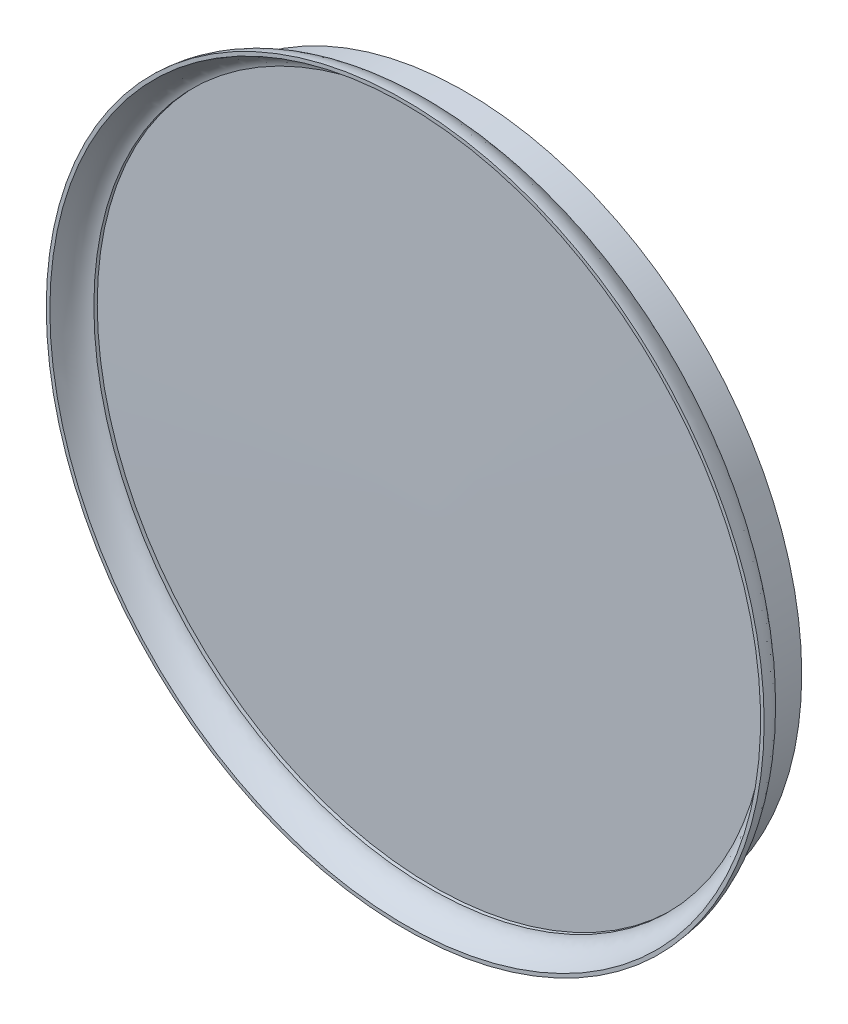
SolidWorks part; units mm, degrees
ref_plane "Front Plane" through (0, 0, 0) normal (0, 0, 1) x (1, 0, 0)
ref_plane "Top Plane" through (0, 0, 0) normal (0, 1, 0) x (1, 0, 0)
ref_plane "Right Plane" through (0, 0, 0) normal (1, 0, 0) x (0, 0, -1)
sketch "Sketch1" plane through (0, 0, 0) normal (0, 0, 1) x (1, 0, 0)
  circle A0 centre (0, 0) radius 44.75
  dimension "D1" = 89.5
extrude "Boss-Extrude1" add sketch "Sketch1" along normal blind 4
sketch "Sketch2" plane through (0, 0, 4) normal (0, 0, 1) x (1, 0, 0)
  circle A0 centre (0, 0) radius 47.75
  circle A1 centre (0, 0) radius 44.75 construction
  dimension "D1" = 3
extrude "Boss-Extrude2" add sketch "Sketch2" along normal blind 4
sketch "Sketch3" plane through (0, 0, 0) normal (1, 0, 0) x (0, 0, -1)
  line L0 (-4, -47.75) -> (-4, 47.75) construction
  line L1 (-4, -44.75) -> (-4, 44.75) construction
  line L2 (-4, 47.75) -> (-4, 44.75)
  line L3 (-4, 47.75) -> (-8, 47.75)
  line L4 (-14.6181, 0) -> (8.5023, 0) construction
  spline S0 degree 2 poles (-4, 44.75) (-5.5166, 47.7003) (-8, 47.75) knots 0 0 0 0.966898 0.966898 0.966898
revolve "Cut-Revolve1" cut sketch "Sketch3" angle 360 about L4
sketch "Sketch4" plane through (0, 0, 0) normal (1, 0, 0) x (0, 0, -1)
  line L1 (-8, 47.75) -> (-8, -47.75) construction
  line L2 (-4.6679, 44.75) -> (-4.2176, 44.75)
  line L3 (-4.2176, 44.75) -> (-4.4427, 0)
  line L4 (-4.4427, 0) -> (-8, 0)
  line L5 (-8, 0) -> (-8, 47.2729)
  spline S0 degree 2 poles (-8, 47.2729) (-5.0207, 46.3587) (-4.6679, 44.75) knots 0 0 0 0.527215 0.527215 0.527215
revolve "Cut-Revolve3" cut sketch "Sketch4" angle 360 about L4
